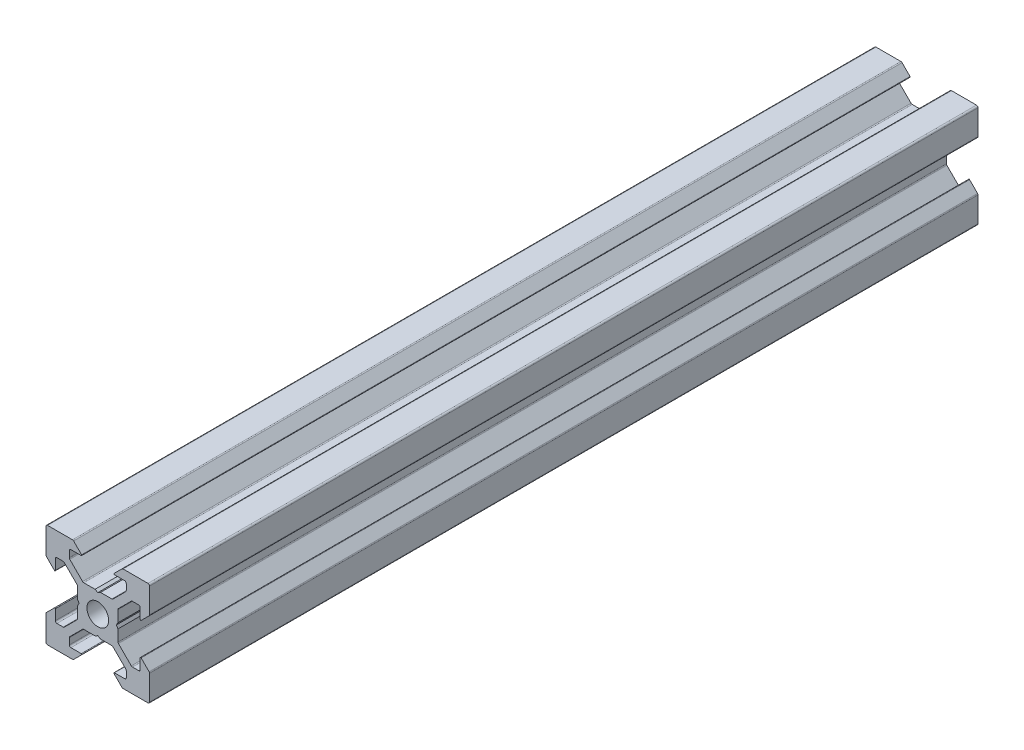
SolidWorks part; units mm, degrees
material "6063-T5"
ref_plane "Plan de face" through (0, 0, 0) normal (0, 0, 1) x (1, 0, 0)
ref_plane "Plan de dessus" through (0, 0, 0) normal (0, 1, 0) x (1, 0, 0)
ref_plane "Plan de droite" through (0, 0, 0) normal (1, 0, 0) x (0, 0, -1)
sketch "Esquisse1" plane through (0, 0, 0) normal (0, 0, 1) x (1, 0, 0)
  line L0 (18.7749, -2.8952) -> (18.7749, -4.8946)
  line L1 (18.4749, -5.1946) -> (17.2591, -5.1946)
  line L2 (17.047, -5.1067) -> (14.5634, -2.6231)
  line L3 (14.4755, -2.411) -> (14.4755, -0.2148)
  line L4 (14.4755, -0.2148) -> (14.1755, 0.3048)
  line L5 (14.1755, 0.3048) -> (14.4755, 0.8244)
  line L6 (14.4755, 0.8244) -> (14.4755, 3.0205)
  line L7 (14.5634, 3.2326) -> (17.047, 5.7162)
  line L8 (17.2591, 5.8041) -> (18.4749, 5.8041)
  line L9 (18.7749, 5.5041) -> (18.7749, 3.5048)
  line L10 (18.9456, 3.4341) -> (20.487, 4.9755)
  line L11 (20.5749, 5.1876) -> (20.5749, 10.0048)
  line L12 (20.2749, 10.3048) -> (15.4577, 10.3048)
  line L13 (15.2456, 10.2169) -> (13.7041, 8.6755)
  line L14 (13.7749, 8.5048) -> (15.7742, 8.5048)
  line L15 (16.0742, 8.2048) -> (16.0742, 6.989)
  line L16 (15.9863, 6.7769) -> (13.5027, 4.2933)
  line L17 (13.2906, 4.2054) -> (11.0945, 4.2054)
  line L18 (11.0945, 4.2054) -> (10.5749, 3.9054)
  line L19 (10.5749, 3.9054) -> (10.0552, 4.2054)
  line L20 (10.0552, 4.2054) -> (7.8591, 4.2054)
  line L21 (7.647, 4.2933) -> (5.1634, 6.7769)
  line L22 (5.0755, 6.989) -> (5.0755, 8.2048)
  line L23 (5.3755, 8.5048) -> (7.3749, 8.5048)
  line L24 (7.4456, 8.6755) -> (5.9041, 10.2169)
  line L25 (5.692, 10.3048) -> (0.8749, 10.3048)
  line L26 (0.5749, 10.0048) -> (0.5749, 5.1876)
  line L27 (0.6627, 4.9755) -> (2.2041, 3.4341)
  line L28 (2.3749, 3.5048) -> (2.3749, 5.5041)
  line L29 (2.6749, 5.8041) -> (3.8906, 5.8041)
  line L30 (4.1027, 5.7162) -> (6.5863, 3.2326)
  line L31 (6.6742, 3.0205) -> (6.6742, 0.8244)
  line L32 (6.6742, 0.8244) -> (6.9742, 0.3048)
  line L33 (6.9742, 0.3048) -> (6.6742, -0.2148)
  line L34 (6.6742, -0.2148) -> (6.6742, -2.411)
  line L35 (6.5863, -2.6231) -> (4.1027, -5.1067)
  line L36 (3.8906, -5.1946) -> (2.6749, -5.1946)
  line L37 (2.3749, -4.8946) -> (2.3749, -2.8952)
  line L38 (2.2041, -2.8245) -> (0.6627, -4.3659)
  line L39 (0.5749, -4.5781) -> (0.5749, -9.3952)
  line L40 (0.8749, -9.6952) -> (5.692, -9.6952)
  line L41 (5.9041, -9.6074) -> (7.4456, -8.0659)
  line L42 (7.3749, -7.8952) -> (5.3755, -7.8952)
  line L43 (5.0755, -7.5952) -> (5.0755, -6.3795)
  line L44 (5.1634, -6.1674) -> (7.647, -3.6838)
  line L45 (7.8591, -3.5959) -> (10.0552, -3.5959)
  line L46 (10.0552, -3.5959) -> (10.5749, -3.2959)
  line L47 (10.5749, -3.2959) -> (11.0945, -3.5959)
  line L48 (11.0945, -3.5959) -> (13.2906, -3.5959)
  line L49 (13.5027, -3.6838) -> (15.9863, -6.1674)
  line L50 (16.0742, -6.3795) -> (16.0742, -7.5952)
  line L51 (15.7742, -7.8952) -> (13.7749, -7.8952)
  line L52 (13.7041, -8.0659) -> (15.2456, -9.6074)
  line L53 (15.4577, -9.6952) -> (20.2749, -9.6952)
  line L54 (20.5749, -9.3952) -> (20.5749, -4.5781)
  line L55 (20.487, -4.3659) -> (18.9456, -2.8245)
  arc A0 (10.5749, -1.7952) -> (12.6749, 0.3048) centre (10.5749, 0.3048) ccw
  arc A1 (12.6749, 0.3048) -> (10.5749, 2.4048) centre (10.5749, 0.3048) ccw
  arc A2 (10.5749, 2.4048) -> (8.4749, 0.3048) centre (10.5749, 0.3048) ccw
  arc A3 (8.4749, 0.3048) -> (10.5749, -1.7952) centre (10.5749, 0.3048) ccw
  arc A4 (18.9456, -2.8245) -> (18.7749, -2.8952) centre (18.8749, -2.8952) ccw
  arc A5 (18.4749, -5.1946) -> (18.7749, -4.8946) centre (18.4749, -4.8946) ccw
  arc A6 (17.047, -5.1067) -> (17.2591, -5.1946) centre (17.2591, -4.8946) ccw
  arc A7 (14.4755, -2.411) -> (14.5634, -2.6231) centre (14.7755, -2.411) ccw
  arc A8 (14.5634, 3.2326) -> (14.4755, 3.0205) centre (14.7755, 3.0205) ccw
  arc A9 (17.2591, 5.8041) -> (17.047, 5.7162) centre (17.2591, 5.5041) ccw
  arc A10 (18.7749, 5.5041) -> (18.4749, 5.8041) centre (18.4749, 5.5041) ccw
  arc A11 (18.7749, 3.5048) -> (18.9456, 3.4341) centre (18.8749, 3.5048) ccw
  arc A12 (20.487, 4.9755) -> (20.5749, 5.1876) centre (20.2749, 5.1876) ccw
  arc A13 (20.5749, 10.0048) -> (20.2749, 10.3048) centre (20.2749, 10.0048) ccw
  arc A14 (15.4577, 10.3048) -> (15.2456, 10.2169) centre (15.4577, 10.0048) ccw
  arc A15 (13.7041, 8.6755) -> (13.7749, 8.5048) centre (13.7749, 8.6048) ccw
  arc A16 (16.0742, 8.2048) -> (15.7742, 8.5048) centre (15.7742, 8.2048) ccw
  arc A17 (15.9863, 6.7769) -> (16.0742, 6.989) centre (15.7742, 6.989) ccw
  arc A18 (13.2906, 4.2054) -> (13.5027, 4.2933) centre (13.2906, 4.5054) ccw
  arc A19 (7.647, 4.2933) -> (7.8591, 4.2054) centre (7.8591, 4.5054) ccw
  arc A20 (5.0755, 6.989) -> (5.1634, 6.7769) centre (5.3755, 6.989) ccw
  arc A21 (5.3755, 8.5048) -> (5.0755, 8.2048) centre (5.3755, 8.2048) ccw
  arc A22 (7.3749, 8.5048) -> (7.4456, 8.6755) centre (7.3749, 8.6048) ccw
  arc A23 (5.9041, 10.2169) -> (5.692, 10.3048) centre (5.692, 10.0048) ccw
  arc A24 (0.8749, 10.3048) -> (0.5749, 10.0048) centre (0.8749, 10.0048) ccw
  arc A25 (0.5749, 5.1876) -> (0.6627, 4.9755) centre (0.8749, 5.1876) ccw
  arc A26 (2.2041, 3.4341) -> (2.3749, 3.5048) centre (2.2749, 3.5048) ccw
  arc A27 (2.6749, 5.8041) -> (2.3749, 5.5041) centre (2.6749, 5.5041) ccw
  arc A28 (4.1027, 5.7162) -> (3.8906, 5.8041) centre (3.8906, 5.5041) ccw
  arc A29 (6.6742, 3.0205) -> (6.5863, 3.2326) centre (6.3742, 3.0205) ccw
  arc A30 (6.5863, -2.6231) -> (6.6742, -2.411) centre (6.3742, -2.411) ccw
  arc A31 (3.8906, -5.1946) -> (4.1027, -5.1067) centre (3.8906, -4.8946) ccw
  arc A32 (2.3749, -4.8946) -> (2.6749, -5.1946) centre (2.6749, -4.8946) ccw
  arc A33 (2.3749, -2.8952) -> (2.2041, -2.8245) centre (2.2749, -2.8952) ccw
  arc A34 (0.6627, -4.3659) -> (0.5749, -4.5781) centre (0.8749, -4.5781) ccw
  arc A35 (0.5749, -9.3952) -> (0.8749, -9.6952) centre (0.8749, -9.3952) ccw
  arc A36 (5.692, -9.6952) -> (5.9041, -9.6074) centre (5.692, -9.3952) ccw
  arc A37 (7.4456, -8.0659) -> (7.3749, -7.8952) centre (7.3749, -7.9952) ccw
  arc A38 (5.0755, -7.5952) -> (5.3755, -7.8952) centre (5.3755, -7.5952) ccw
  arc A39 (5.1634, -6.1674) -> (5.0755, -6.3795) centre (5.3755, -6.3795) ccw
  arc A40 (7.8591, -3.5959) -> (7.647, -3.6838) centre (7.8591, -3.8959) ccw
  arc A41 (13.5027, -3.6838) -> (13.2906, -3.5959) centre (13.2906, -3.8959) ccw
  arc A42 (16.0742, -6.3795) -> (15.9863, -6.1674) centre (15.7742, -6.3795) ccw
  arc A43 (15.7742, -7.8952) -> (16.0742, -7.5952) centre (15.7742, -7.5952) ccw
  arc A44 (13.7749, -7.8952) -> (13.7041, -8.0659) centre (13.7749, -7.9952) ccw
  arc A45 (15.2456, -9.6074) -> (15.4577, -9.6952) centre (15.4577, -9.3952) ccw
  arc A46 (20.2749, -9.6952) -> (20.5749, -9.3952) centre (20.2749, -9.3952) ccw
  arc A47 (20.5749, -4.5781) -> (20.487, -4.3659) centre (20.2749, -4.5781) ccw
extrude "Boss.-Extru.1" add sketch "Esquisse1" along normal blind 160
